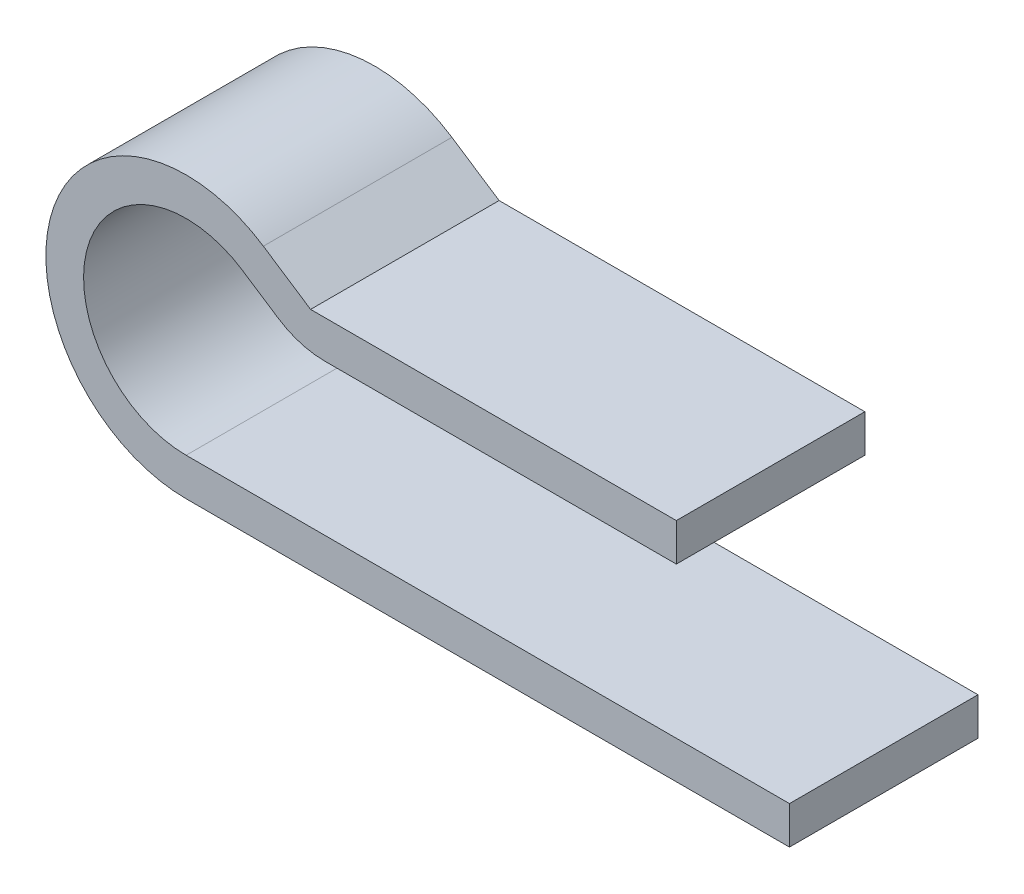
SolidWorks part; units mm, degrees
material "Brass"
ref_plane "Front Plane" through (0, 0, 0) normal (0, 0, 1) x (1, 0, 0)
ref_plane "Top Plane" through (0, 0, 0) normal (0, 1, 0) x (1, 0, 0)
ref_plane "Right Plane" through (0, 0, 0) normal (1, 0, 0) x (0, 0, -1)
sketch "Sketch1" plane through (0, 0, 0) normal (0, 0, 1) x (1, 0, 0)
  line L0 (-1.6, 0) -> (1.6, 0)
  line L1 (-1.3451, 0) -> (1.6, 0) construction
  line L2 (-1.4247, -0.2) -> (1.6, -0.2) construction
  line L3 (-1.3006, 0.9982) -> (-1, 0.8)
  line L4 (-1, 0.8) -> (1, 0.8)
  line L5 (-0.94, 1) -> (1, 1)
  line L6 (-1.1905, 1.1651) -> (-0.94, 1)
  line L8 (-1.6, -0.2) -> (1.6, -0.2)
  line L9 (1, 1) -> (1, 0.8)
  line L10 (1.6, 0) -> (1.6, -0.2)
  line L12 (-1.3451, 0) -> (-1.3897, 0.0423) construction
  line L13 (-1.4247, -0.2) -> (-1.4425, -0.1831) construction
  arc A0 (-1.6, 0) -> (-1.3006, 0.9982) centre (-1.6, 0.544) cw
  arc A1 (-1.6, -0.2) -> (-1.1905, 1.1651) centre (-1.6, 0.544) cw
  arc A2 (-1.3897, 0.0423) -> (-1.3006, 0.9982) centre (-1.6, 0.544) cw construction
  arc A3 (-1.4425, -0.1831) -> (-1.1905, 1.1651) centre (-1.6, 0.544) cw construction
  point P3 (0, 0)
  point P9 (0, 0.8)
  dimension "D1" = 3.2
  dimension "D2" = 0.3
  dimension "D4" = 0.8
  dimension "D5" = 2
  dimension "D6" = 0.2
extrude "Boss-Extrude1" add sketch "Sketch1" along normal blind 1
fillet "Fillet2" radius 0.45 1 edges at (-1, 0.8, 0.5)
